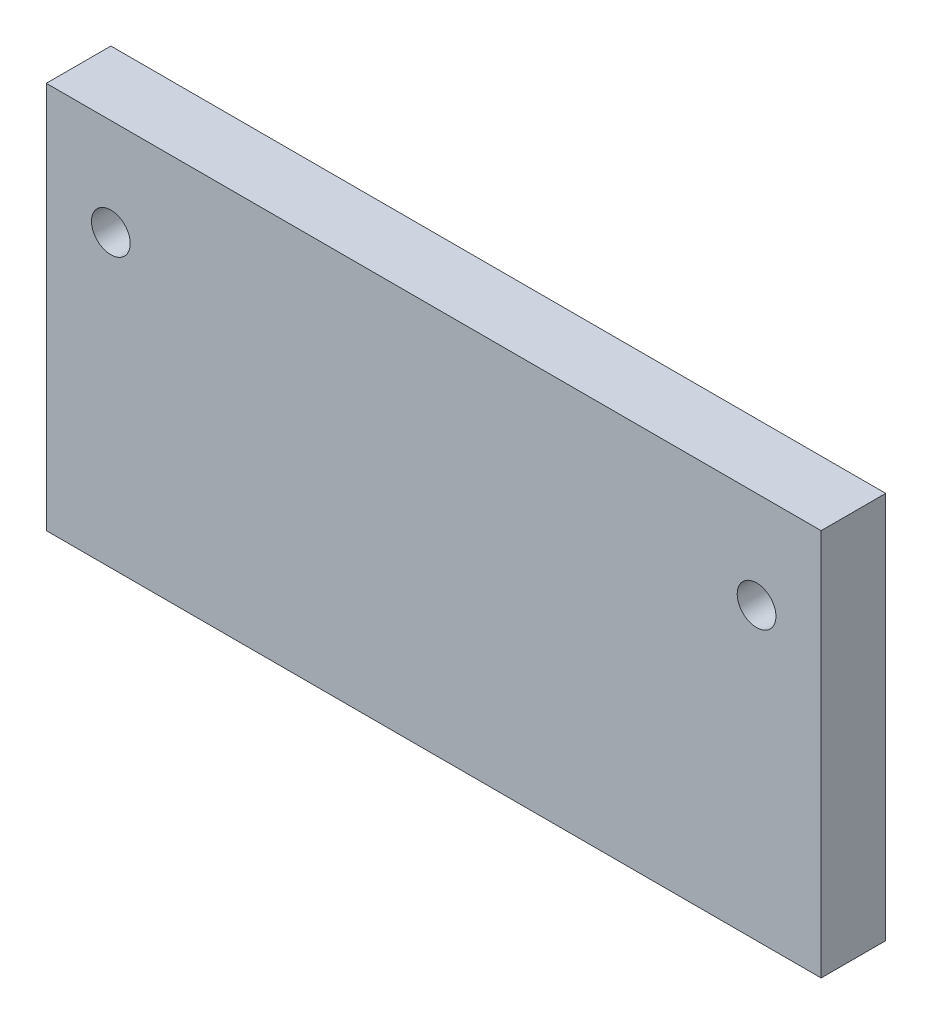
SolidWorks part; units mm, degrees
material "ABS"
ref_plane "前视基准面" through (0, 0, 0) normal (0, 0, 1) x (1, 0, 0)
ref_plane "上视基准面" through (0, 0, 0) normal (0, 1, 0) x (1, 0, 0)
ref_plane "右视基准面" through (0, 0, 0) normal (1, 0, 0) x (0, 0, -1)
sketch "草图2" plane through (0, 0, -5.6802) normal (0, 0, -1) x (-1, 0, 0)
  line L0 (-76.7207, 15) -> (23.2793, 15) construction
  line L1 (23.2793, 15) -> (23.2793, 0) construction
  line L2 (3.2793, 15) -> (-56.7207, 15)
  line L3 (3.2793, 15) -> (3.2793, -15)
  line L4 (3.2793, -15) -> (-56.7207, -15)
  line L5 (-56.7207, 15) -> (-56.7207, -15)
  circle A0 centre (-51.7207, 7.5) radius 1.5
  circle A1 centre (-1.7207, 7.5) radius 1.5
  point P8 (23.2793, 7.5)
  dimension "D1" = 60
  dimension "D2" = 20
  dimension "D3" = 30
extrude "凸台-拉伸1" add sketch "草图2" along normal blind 5
